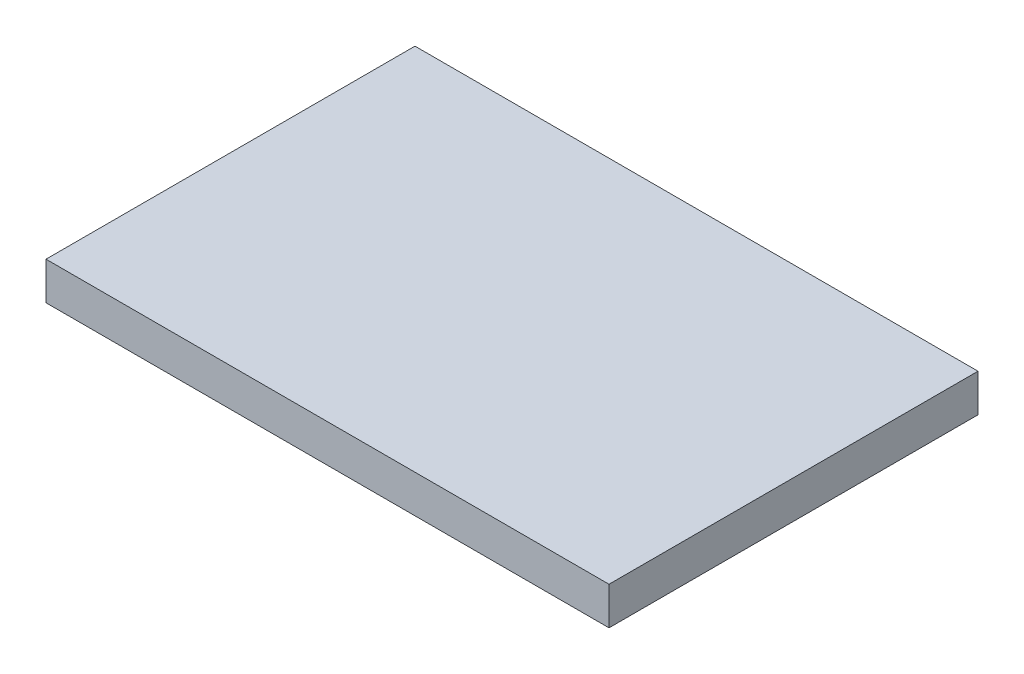
SolidWorks part; units mm, degrees
ref_plane "Front Plane" through (0, 0, 0) normal (0, 0, 1) x (1, 0, 0)
ref_plane "Top Plane" through (0, 0, 0) normal (0, 1, 0) x (1, 0, 0)
ref_plane "Right Plane" through (0, 0, 0) normal (1, 0, 0) x (0, 0, -1)
sketch "Sketch1" plane through (0, 0, 0) normal (0, 1, 0) x (1, 0, 0)
  line L1 (-7.675, 5.03) -> (7.675, 5.03)
  line L2 (-7.675, 5.03) -> (-7.675, -5.03)
  line L3 (-7.675, -5.03) -> (7.675, -5.03)
  line L4 (7.675, 5.03) -> (7.675, -5.03)
  line L5 (-7.675, 5.03) -> (7.675, -5.03) construction
  line L6 (-7.675, -5.03) -> (7.675, 5.03) construction
  point P0 (0, 0)
  dimension "D1" = 15.35
  dimension "D2" = 10.06
extrude "Boss-Extrude1" add sketch "Sketch1" along normal blind 1.03
